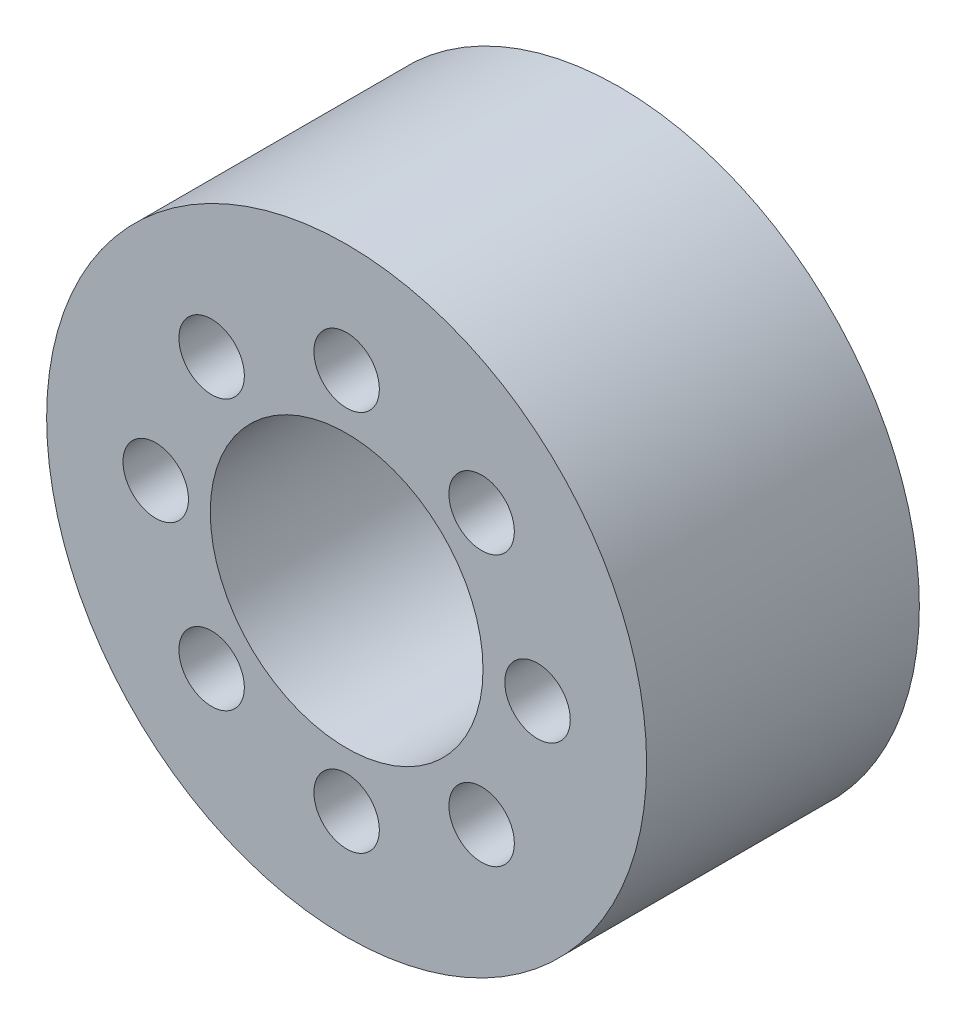
SolidWorks part; units mm, degrees
ref_plane "Plan de face" through (0, 0, 0) normal (0, 0, 1) x (1, 0, 0)
ref_plane "Plan de dessus" through (0, 0, 0) normal (0, 1, 0) x (1, 0, 0)
ref_plane "Plan de droite" through (0, 0, 0) normal (1, 0, 0) x (0, 0, -1)
sketch "Esquisse1" plane through (0, 0, 0) normal (0, 0, 1) x (1, 0, 0)
  circle A0 centre (0, 0) radius 11
  circle A1 centre (0, 0) radius 5
  dimension "D1" = 22
  dimension "D2" = 10
extrude "Boss.-Extru.1" add sketch "Esquisse1" along normal blind 10
hole_wizard "Dégagement M21" positions "Esquisse2" profile "Esquisse3" hole size "M2" standard "ISO" end condition up to next
sketch "Esquisse2" plane through (0, 0, 10) normal (0, 0, 1) x (1, 0, 0)
  point P0 (0, 7)
  point P8 (4.9497, 4.9497)
  point P9 (7, 0)
  point P10 (4.9497, -4.9497)
  point P11 (0, -7)
  point P12 (-4.9497, -4.9497)
  point P13 (-7, 0)
  point P14 (-4.9497, 4.9497)
  point P15 (0, 0)
  dimension "D1" = 7
  dimension "D2" = 8
sketch "Esquisse3" plane through (0, 7, 10) normal (1, 0, 0) x (0, -1, 0)
  line L0 (0, 0) -> (0, 10)
  line L1 (0, 10) -> (1.2, 10)
  line L2 (1.2, 10) -> (1.2, 0)
  line L5 (1.2, 0) -> (0, 0)
  line L11 (0, -6.35) -> (0, 107.95) construction
  dimension "Diamètre du perçage jusqu'au prochain" = 2.4
  dimension "Profondeur du perçage jusqu'au prochain" = 10
